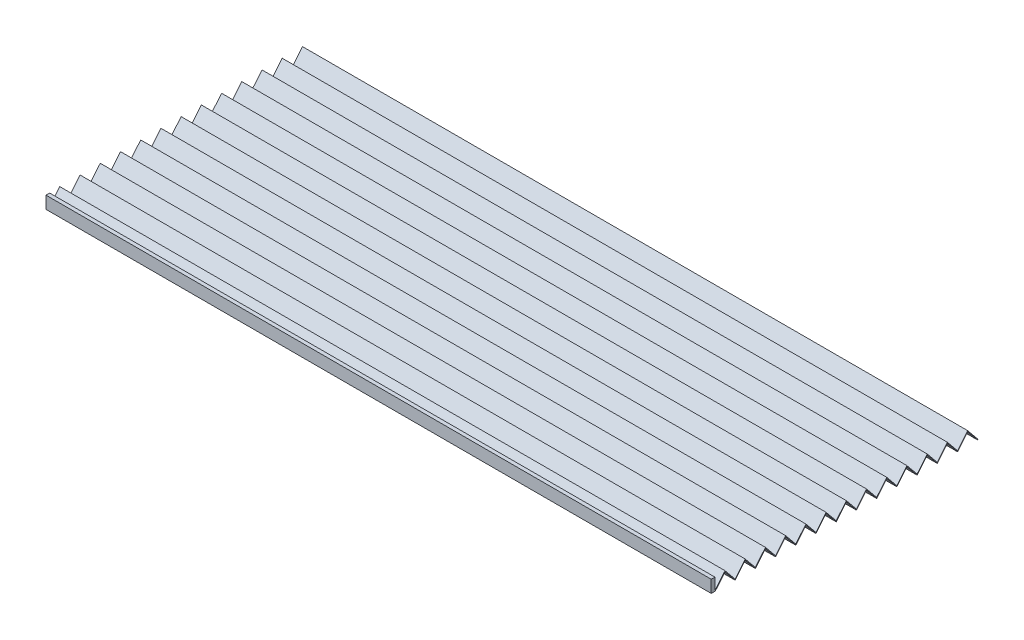
SolidWorks part; units mm, degrees
ref_plane "Front Plane" through (0, 0, 0) normal (0, 0, 1) x (1, 0, 0)
ref_plane "Top Plane" through (0, 0, 0) normal (0, 1, 0) x (1, 0, 0)
ref_plane "Right Plane" through (0, 0, 0) normal (1, 0, 0) x (0, 0, -1)
sketch "Sketch2" plane through (0, 0, 0) normal (0, 0, 1) x (1, 0, 0)
  line L1 (-270, 10) -> (270, 10)
  line L2 (-270, 10) -> (-270, 0)
  line L3 (-270, 0) -> (270, 0)
  line L4 (270, 10) -> (270, 0)
  point P4 (0, 0)
  dimension "D1" = 10
  dimension "D2" = 540
extrude "Boss-Extrude1" add sketch "Sketch2" along normal blind 3
sketch "Sketch3" plane through (270, 0, 0) normal (1, 0, 0) x (0, 0, -1)
  line L0 (0, 10) -> (213.3594, 10) construction
  line L1 (0, 0) -> (213.3594, 0) construction
  line L2 (213.3594, 10) -> (213.3594, 0) construction
  line L3 (0, 0) -> (8.2061, 10)
  line L4 (8.2061, 10) -> (16.4123, 0)
  line L5 (16.4123, 0) -> (24.6184, 10)
  line L6 (24.6184, 10) -> (32.8245, 0)
  line L7 (32.8245, 0) -> (41.0307, 10)
  line L8 (41.0307, 10) -> (49.2368, 0)
  line L9 (49.2368, 0) -> (57.4429, 10)
  line L10 (57.4429, 10) -> (65.6491, 0)
  line L11 (65.6491, 0) -> (73.8552, 10)
  line L12 (73.8552, 10) -> (82.0613, 0)
  line L13 (82.0613, 0) -> (90.2675, 10)
  line L14 (90.2675, 10) -> (98.4736, 0)
  line L15 (98.4736, 0) -> (106.6797, 10)
  line L16 (106.6797, 10) -> (114.8859, 0)
  line L17 (114.8859, 0) -> (123.092, 10)
  line L18 (123.092, 10) -> (131.2981, 0)
  line L20 (131.2981, 0) -> (139.5043, 10)
  line L21 (139.5043, 10) -> (147.7104, 0)
  line L22 (147.7104, 0) -> (155.9165, 10)
  line L23 (155.9165, 10) -> (164.1226, 0)
  line L24 (164.1226, 0) -> (172.3288, 10)
  line L25 (172.3288, 10) -> (180.5349, 0)
  line L26 (180.5349, 0) -> (188.741, 10)
  line L27 (188.741, 10) -> (196.9472, 0)
  line L28 (196.9472, 0) -> (205.1533, 10)
  line L29 (205.1533, 10) -> (213.3594, 0)
  line L30 (213.3594, 10) -> (213.3594, 0) construction
extrude "Extrude-Thin1" add sketch "Sketch3" against normal through all thin thin type mid plane wall 0.5
